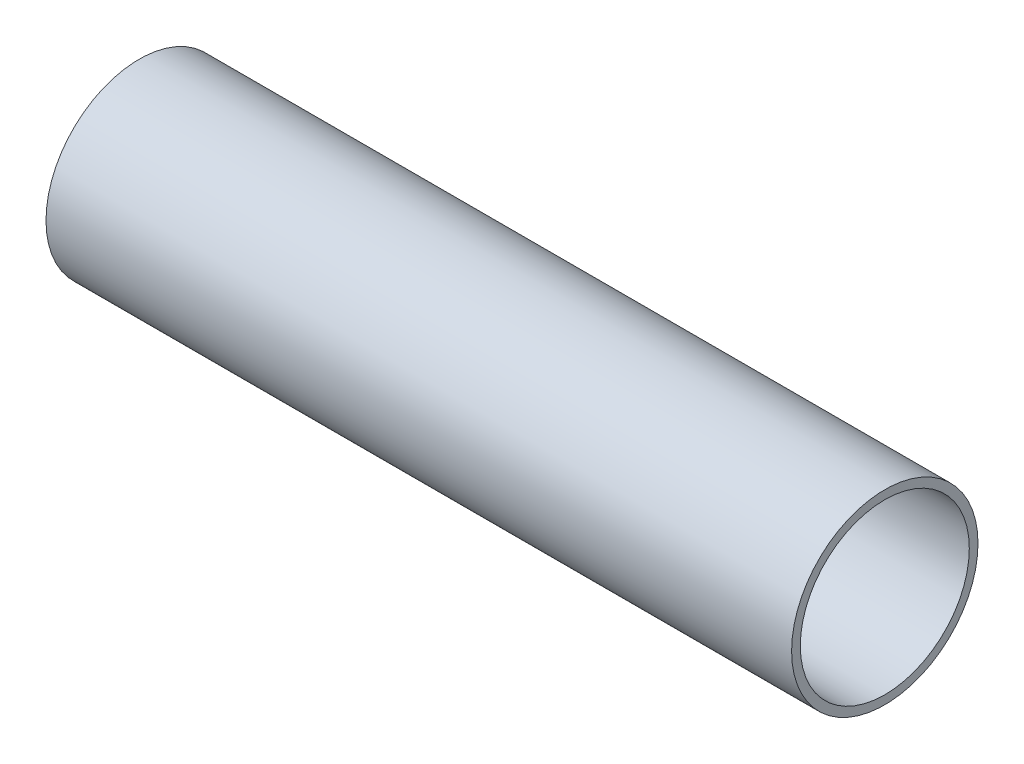
SolidWorks part; units mm, degrees
ref_plane "Front Plane" through (0, 0, 0) normal (0, 0, 1) x (1, 0, 0)
ref_plane "Top Plane" through (0, 0, 0) normal (0, 1, 0) x (1, 0, 0)
ref_plane "Right Plane" through (0, 0, 0) normal (1, 0, 0) x (0, 0, -1)
sketch "Sketch1" plane through (0, 0, 0) normal (0, 1, 0) x (1, 0, 0)
  line L0 (0, 0) -> (127, 0) construction
  line L1 (0, 9.525) -> (76.2, 9.525)
  line L2 (76.2, 9.525) -> (76.2, 8.636)
  line L3 (76.2, 8.636) -> (0, 8.636)
  line L4 (0, 8.636) -> (0, 9.525)
  dimension "D1" = 127
  dimension "D2" = 9.525
  dimension "D3" = 0.889
  dimension "D4" = 76.2
revolve "Revolve1" add sketch "Sketch1" angle 360 about L0
